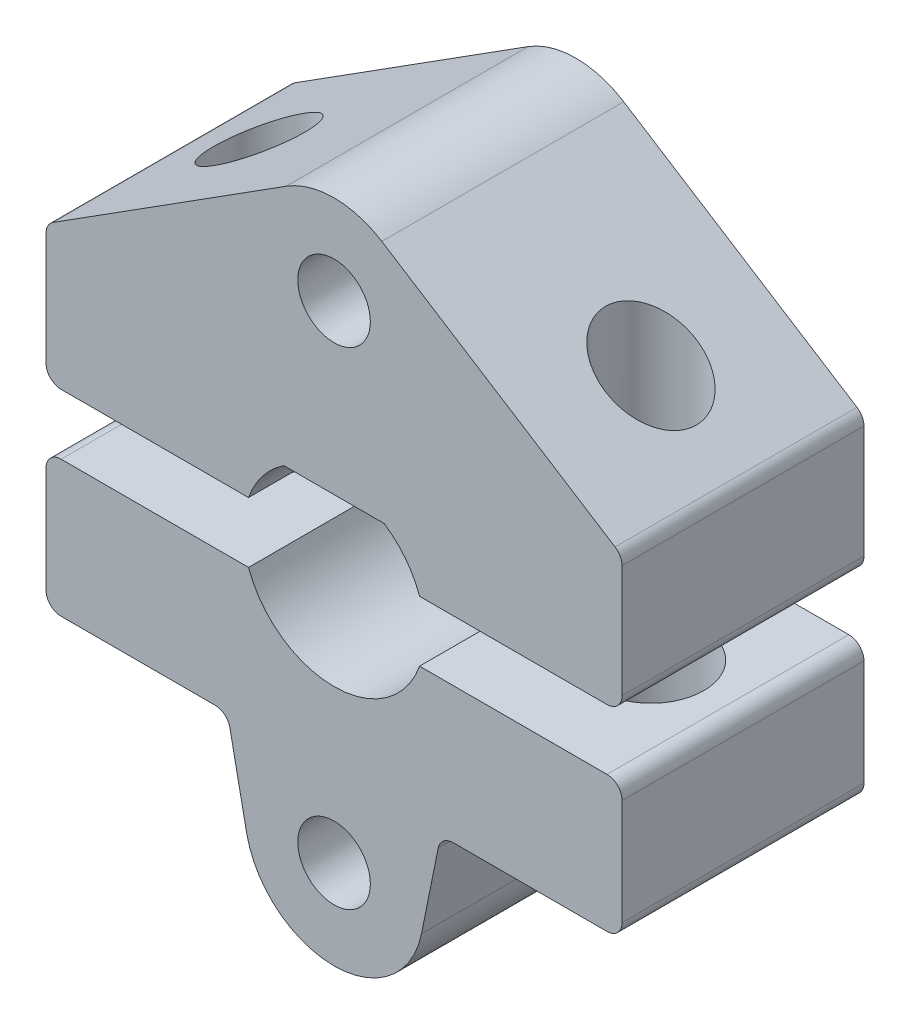
SolidWorks part; units mm, degrees
material "6061-T6 (SS)"
ref_plane "前视基准面" through (0, 0, 0) normal (0, 0, 1) x (1, 0, 0)
ref_plane "上视基准面" through (0, 0, 0) normal (0, 1, 0) x (1, 0, 0)
ref_plane "右视基准面" through (0, 0, 0) normal (1, 0, 0) x (0, 0, -1)
sketch "草图1" plane through (0, 0, 0) normal (0, 0, 1) x (1, 0, 0)
  line L0 (-1.6583, 2.5) -> (1.6583, 2.5)
  line L1 (-9.2941, 5.6473) -> (-1.5803, 10.541)
  line L2 (1.5803, 10.541) -> (9.2941, 5.6473)
  line L3 (-9.5263, 5.2251) -> (-9.5263, 1.5)
  line L4 (-9.0263, 1) -> (-2.8284, 1)
  line L5 (9.5263, 1.5) -> (9.5263, 5.2251)
  line L6 (0, 1) -> (0, 0) construction
  line L7 (-9.0263, -1) -> (-2.8284, -1)
  line L8 (9.5263, -1.5) -> (9.5263, -5)
  line L9 (9.0263, -5.5) -> (3.9352, -5.5)
  line L10 (3.4451, -5.9008) -> (2.8913, -8.6355)
  line L11 (-2.8913, -8.6355) -> (-3.4451, -5.9008)
  line L12 (-3.9352, -5.5) -> (-9.0263, -5.5)
  line L13 (-9.5263, -5) -> (-9.5263, -1.5)
  line L14 (0, 0) -> (0, -1) construction
  line L15 (2.8284, 1) -> (9.0263, 1)
  line L16 (2.8284, -1) -> (9.0263, -1)
  line L17 (9.2941, 5.6473) -> (9.5263, 5.5) construction
  line L18 (9.5263, 5.5) -> (9.5263, 5.2251) construction
  arc A0 (-1.6583, 2.5) -> (-2.8284, 1) centre (0, 0) ccw
  circle A1 centre (0, 0) radius 8.05 construction
  circle A2 centre (0, 8.05) radius 1.2
  circle A3 centre (0, -8.05) radius 1.2
  arc A4 (-1.5803, 10.541) -> (1.5803, 10.541) centre (0, 8.05) cw
  circle A5 centre (0, 0) radius 11 construction
  arc A6 (2.8913, -8.6355) -> (-2.8913, -8.6355) centre (0, -8.05) cw
  arc A7 (-9.5263, 1.5) -> (-9.0263, 1) centre (-9.0263, 1.5) ccw
  arc A8 (-9.2941, 5.6473) -> (-9.5263, 5.2251) centre (-9.0263, 5.2251) ccw
  arc A9 (9.2941, 5.6473) -> (9.5263, 5.2251) centre (9.0263, 5.2251) cw
  arc A10 (9.0263, 1) -> (9.5263, 1.5) centre (9.0263, 1.5) ccw
  arc A11 (-9.0263, -5.5) -> (-9.5263, -5) centre (-9.0263, -5) cw
  arc A12 (-9.0263, -1) -> (-9.5263, -1.5) centre (-9.0263, -1.5) ccw
  arc A13 (9.5263, -5) -> (9.0263, -5.5) centre (9.0263, -5) cw
  arc A14 (9.0263, -1) -> (9.5263, -1.5) centre (9.0263, -1.5) cw
  arc A15 (3.9352, -5.5) -> (3.4451, -5.9008) centre (3.9352, -6) ccw
  arc A16 (-3.4451, -5.9008) -> (-3.9352, -5.5) centre (-3.9352, -6) ccw
  arc A17 (-2.8284, -1) -> (2.8284, -1) centre (0, 0) ccw
  arc A18 (2.8284, 1) -> (1.6583, 2.5) centre (0, 0) ccw
  point P31 (-9.5263, 1)
  point P34 (-9.5263, 5.5)
  point P39 (9.5263, 1)
  point P42 (-9.5263, -5.5)
  point P47 (9.5263, -5.5)
  point P52 (3.5263, -5.5)
  dimension "D1" = 16.1
  dimension "D2" = 6
  dimension "D4" = 2.4
  dimension "D6" = 22
  dimension "D10" = 0.5
  dimension "D5" = 4.5
  dimension "D3" = 2.5
  dimension "D7" = 1
  dimension "D9" = 6
extrude "凸台-拉伸1" add sketch "草图1" along normal blind 8
cosmetic thread "装饰螺纹线3" parameters "D2"=3
sketch "草图2" plane through (0, -5.5, 0) normal (0, -1, 0) x (1, 0, 0)
  line L0 (-9.5263, 4) -> (-6.4807, 4) construction
  line L1 (-9.5263, 8) -> (-9.5263, 0) construction
  line L2 (-6.4807, 4) -> (6.4807, 4) construction
  line L3 (6.4807, 4) -> (9.5263, 4) construction
  line L4 (9.5263, 8) -> (9.5263, 0) construction
  line L5 (6.4807, 8) -> (6.4807, 4) construction
  line L6 (3.9352, 8) -> (9.0263, 8) construction
  circle A0 centre (6.4807, 4) radius 1.5
  circle A1 centre (-6.4807, 4) radius 1.5
  dimension "D1" = 3
extrude "切除-拉伸1" cut sketch "草图2" against normal through all
cosmetic thread "装饰螺纹线1" parameters "D2"=3
cosmetic thread "装饰螺纹线2" parameters "D2"=3
sketch "草图3" plane through (0, -5.5, 0) normal (0, -1, 0) x (1, 0, 0)
  circle A0 centre (-6.4807, 4) radius 1.75
  circle A1 centre (6.4807, 4) radius 1.75
  dimension "D1" = 3.5
extrude "切除-拉伸2" cut sketch "草图3" against normal up to surface (4.5 mm away) up to face at (-4.9807, -1, 4)
